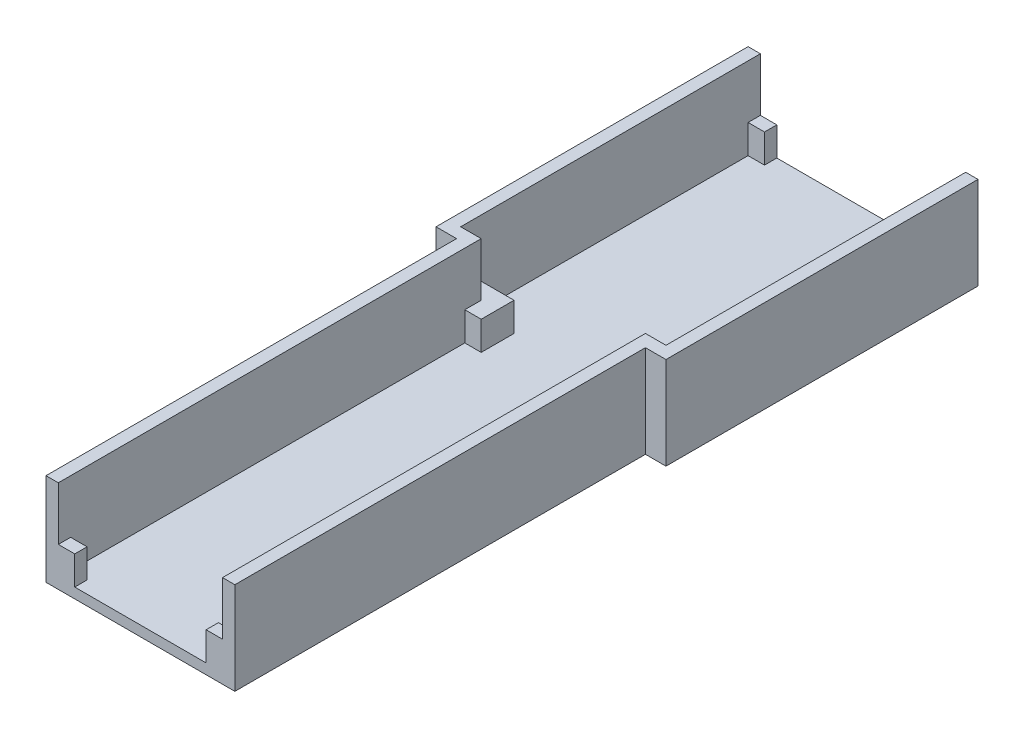
SolidWorks part; units mm, degrees
ref_plane "Front Plane" through (0, 0, 0) normal (0, 0, 1) x (1, 0, 0)
ref_plane "Top Plane" through (0, 0, 0) normal (0, 1, 0) x (1, 0, 0)
ref_plane "Right Plane" through (0, 0, 0) normal (1, 0, 0) x (0, 0, -1)
sketch "Sketch1" plane through (0, 0, 0) normal (0, 1, 0) x (1, 0, 0)
  line L1 (21.9955, 25.8604) -> (77.9955, 25.8604)
  line L2 (21.9955, 25.8604) -> (21.9955, -47.1396)
  line L3 (21.9955, -47.1396) -> (77.9955, -47.1396)
  line L4 (77.9955, 25.8604) -> (77.9955, -47.1396)
  line L5 (26.9955, -47.1396) -> (72.9955, -47.1396)
  line L6 (26.9955, -47.1396) -> (26.9955, -150.1396)
  line L7 (26.9955, -150.1396) -> (72.9955, -150.1396)
  line L8 (72.9955, -47.1396) -> (72.9955, -150.1396)
  dimension "D1" = 73
  dimension "D2" = 56
  dimension "D3" = 103
  dimension "D4" = 46
  dimension "D5" = 5
extrude "Boss-Extrude2" add sketch "Sketch1" along normal blind 2.5 contours L8 L3 L6 L7 | L4 L1 L2 L3
sketch "Sketch3" plane through (0, 2.5, 0) normal (0, 1, 0) x (1, 0, 0)
  line L0 (21.9955, 25.8604) -> (77.9955, 25.8604) construction
  line L1 (24.9955, 22.8604) -> (74.9955, 22.8604)
  line L2 (24.9955, 22.8604) -> (24.9955, -47.1396)
  line L3 (24.9955, -47.1396) -> (74.9955, -47.1396)
  line L4 (74.9955, 22.8604) -> (74.9955, -47.1396)
  line L5 (29.9955, -47.1396) -> (69.9955, -47.1396)
  line L6 (29.9955, -47.1396) -> (29.9955, -147.1396)
  line L7 (29.9955, -147.1396) -> (69.9955, -147.1396)
  line L8 (69.9955, -47.1396) -> (69.9955, -147.1396)
  line L9 (77.9955, 25.8604) -> (77.9955, -47.1396) construction
  line L10 (21.9955, 25.8604) -> (21.9955, -47.1396) construction
  line L11 (26.9955, -150.1396) -> (72.9955, -150.1396) construction
  line L12 (72.9955, -47.1396) -> (72.9955, -150.1396) construction
  line L13 (26.9955, -47.1396) -> (26.9955, -150.1396) construction
  line M7 (72.9955, -150.1396) -> (72.9955, -47.1396)
  line M8 (72.9955, -47.1396) -> (77.9955, -47.1396)
  line M9 (77.9955, -47.1396) -> (77.9955, 25.8604)
  line M10 (77.9955, 25.8604) -> (21.9955, 25.8604)
  line M11 (21.9955, 25.8604) -> (21.9955, -47.1396)
  line M12 (21.9955, -47.1396) -> (26.9955, -47.1396)
  line M13 (26.9955, -47.1396) -> (26.9955, -150.1396)
  line M14 (26.9955, -150.1396) -> (72.9955, -150.1396)
  dimension "D1" = 3
  dimension "D2" = 3
  dimension "D3" = 3
  dimension "D4" = 3
  dimension "D5" = 3
  dimension "D6" = 3
  dimension "D7" = 70
extrude "Boss-Extrude3" add sketch "Sketch3" along normal blind 20 contours L1 L4 L2 M8 M9 M10 M11 M12 | L3 L8 L7 L6 M13 M14 M7
sketch "Sketch4" plane through (26.9955, 0, 0) normal (-1, 0, 0) x (0, 0, 1)
  line L0 (47.1396, 0) -> (150.1396, 0) construction
  line L1 (47.1396, 22.5) -> (50.1396, 22.5)
  line L2 (47.1396, 22.5) -> (47.1396, 0)
  line L3 (47.1396, 0) -> (50.1396, 0)
  line L4 (50.1396, 22.5) -> (50.1396, 0)
  dimension "D1" = 3
extrude "Boss-Extrude4" add sketch "Sketch4" along normal blind 5
sketch "Sketch7" plane through (72.9955, 0, 0) normal (1, 0, 0) x (0, 0, -1)
  line L0 (-47.1396, 0) -> (-150.1396, 0) construction
  line L1 (-47.1396, 22.5) -> (-50.1396, 22.5)
  line L2 (-47.1396, 22.5) -> (-47.1396, 0)
  line L3 (-47.1396, 0) -> (-50.1396, 0)
  line L4 (-50.1396, 22.5) -> (-50.1396, 0)
  dimension "D1" = 3
extrude "Boss-Extrude5" add sketch "Sketch7" along normal blind 5
sketch "Sketch8" plane through (0, 22.5, 0) normal (0, 1, 0) x (1, 0, 0)
  line L0 (77.9955, 25.8604) -> (21.9955, 25.8604) construction
  line L1 (24.9955, 22.8604) -> (28.9955, 22.8604)
  line L2 (24.9955, 22.8604) -> (24.9955, 25.8604)
  line L3 (24.9955, 25.8604) -> (28.9955, 25.8604)
  line L4 (28.9955, 22.8604) -> (28.9955, 25.8604)
  line L5 (26.9955, -150.1396) -> (72.9955, -150.1396) construction
  line L6 (74.9955, 22.8604) -> (70.9955, 22.8604)
  line L7 (74.9955, 22.8604) -> (74.9955, 25.8604)
  line L8 (74.9955, 25.8604) -> (70.9955, 25.8604)
  line L9 (70.9955, 22.8604) -> (70.9955, 25.8604)
  line L10 (69.9955, -147.1396) -> (65.9955, -147.1396)
  line L11 (69.9955, -147.1396) -> (69.9955, -150.1396)
  line L12 (69.9955, -150.1396) -> (65.9955, -150.1396)
  line L13 (65.9955, -147.1396) -> (65.9955, -150.1396)
  line L15 (29.9955, -147.1396) -> (33.9955, -147.1396)
  line L16 (29.9955, -147.1396) -> (29.9955, -150.1396)
  line L17 (29.9955, -150.1396) -> (33.9955, -150.1396)
  line L18 (33.9955, -147.1396) -> (33.9955, -150.1396)
  line L19 (33.9955, -147.1396) -> (65.9955, -147.1396)
  line L20 (33.9955, -147.1396) -> (33.9955, -150.1396)
  line L21 (33.9955, -150.1396) -> (65.9955, -150.1396)
  line L22 (65.9955, -147.1396) -> (65.9955, -150.1396)
  line L23 (28.9955, 25.8604) -> (70.9955, 25.8604)
  line L24 (28.9955, 25.8604) -> (28.9955, 22.8604)
  line L25 (28.9955, 22.8604) -> (70.9955, 22.8604)
  line L26 (70.9955, 25.8604) -> (70.9955, 22.8604)
  line M8 (77.9955, 25.8604) -> (21.9955, 25.8604)
  line M12 (26.9955, -150.1396) -> (72.9955, -150.1396)
  line M14 (24.9955, 22.8604) -> (74.9955, 22.8604)
  line M18 (69.9955, -147.1396) -> (29.9955, -147.1396)
  dimension "D1" = 4
  dimension "D2" = 4
  dimension "D3" = 4
  dimension "D4" = 4
extrude "Cut-Extrude1" cut sketch "Sketch8" against normal blind 13 contours L4 L2 M14 M8 | L9 L7 M14 M8 | L13 L11 M18 M12 | L18 L16 M18 M12
sketch "Sketch9" plane through (0, 22.5, 0) normal (0, 1, 0) x (1, 0, 0)
  line L1 (28.9955, 25.8604) -> (70.9955, 25.8604)
  line L2 (28.9955, 25.8604) -> (28.9955, 22.8604)
  line L3 (28.9955, 22.8604) -> (70.9955, 22.8604)
  line L4 (70.9955, 25.8604) -> (70.9955, 22.8604)
extrude "Cut-Extrude2" cut sketch "Sketch9" against normal blind 20
sketch "Sketch10" plane through (0, 22.5, 0) normal (0, 1, 0) x (1, 0, 0)
  line L1 (33.9955, -147.1396) -> (65.9955, -147.1396)
  line L2 (33.9955, -147.1396) -> (33.9955, -150.1396)
  line L3 (33.9955, -150.1396) -> (65.9955, -150.1396)
  line L4 (65.9955, -147.1396) -> (65.9955, -150.1396)
extrude "Cut-Extrude3" cut sketch "Sketch10" against normal blind 20
sketch "Sketch11" plane through (0, 2.5, 0) normal (0, 1, 0) x (1, 0, 0)
  line L0 (24.9955, 22.8604) -> (24.9955, -47.1396) construction
  line L1 (29.9955, -47.1396) -> (33.9955, -47.1396)
  line L2 (29.9955, -47.1396) -> (29.9955, -51.1396)
  line L3 (29.9955, -51.1396) -> (33.9955, -51.1396)
  line L4 (33.9955, -47.1396) -> (33.9955, -51.1396)
  line L5 (69.9955, -47.1396) -> (65.9955, -47.1396)
  line L6 (69.9955, -47.1396) -> (69.9955, -51.1396)
  line L7 (69.9955, -51.1396) -> (65.9955, -51.1396)
  line L8 (65.9955, -47.1396) -> (65.9955, -51.1396)
  line L9 (33.9955, -47.1396) -> (24.9955, -47.1396)
  line L10 (33.9955, -47.1396) -> (33.9955, -43.1396)
  line L11 (33.9955, -43.1396) -> (24.9955, -43.1396)
  line L12 (24.9955, -47.1396) -> (24.9955, -43.1396)
  line L13 (74.9955, 22.8604) -> (74.9955, -47.1396) construction
  line L14 (65.9955, -47.1396) -> (74.9955, -47.1396)
  line L15 (65.9955, -47.1396) -> (65.9955, -43.1396)
  line L16 (65.9955, -43.1396) -> (74.9955, -43.1396)
  line L17 (74.9955, -47.1396) -> (74.9955, -43.1396)
  line M8 (69.9955, -147.1396) -> (69.9955, -47.1396)
  line M9 (69.9955, -47.1396) -> (74.9955, -47.1396)
  line M10 (74.9955, -47.1396) -> (74.9955, 22.8604)
  line M16 (24.9955, 22.8604) -> (24.9955, -47.1396)
  line M17 (24.9955, -47.1396) -> (29.9955, -47.1396)
  line M18 (29.9955, -47.1396) -> (29.9955, -147.1396)
  dimension "D1" = 4
  dimension "D2" = 4
  dimension "D3" = 4
  dimension "D4" = 4
  dimension "D5" = 4
  dimension "D6" = 4
extrude "Boss-Extrude6" add sketch "Sketch11" along normal blind 7 contours L4 L1 L3 M18 | L10 L11 L1 M16 M17 | L16 L15 L5 M9 M10 | L5 L8 L7 M8
